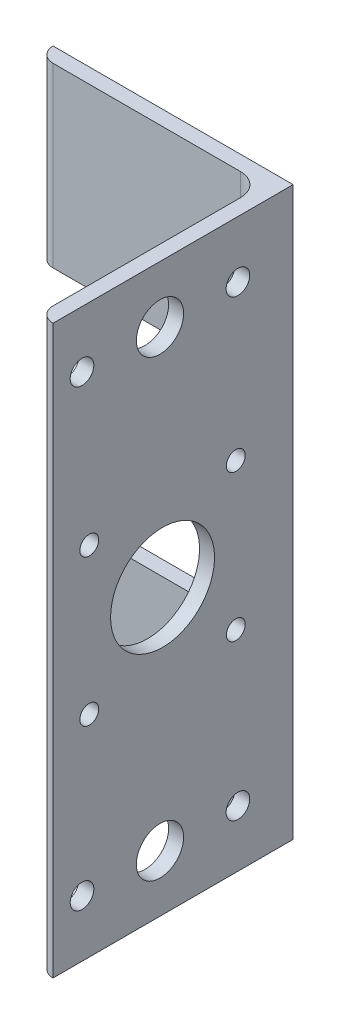
SolidWorks part; units mm, degrees
ref_plane "Alzado" through (0, 0, 0) normal (0, 0, 1) x (1, 0, 0)
ref_plane "Planta" through (0, 0, 0) normal (0, 1, 0) x (1, 0, 0)
ref_plane "Vista lateral" through (0, 0, 0) normal (1, 0, 0) x (0, 0, -1)
sketch "Croquis1" plane through (0, 0, 0) normal (0, 0, 1) x (1, 0, 0)
  line L0 (0, 0) -> (0, 120)
  dimension "D1" = 120
other "Hierro angular 2 X 2 X 0.125(1)"
ref_plane "Plano1" through (0, 0, 0) normal (0, 1, 0) x (-1, 0, 0)
sketch "Sketch1" plane through (0, 0, 0) normal (0, 1, 0) x (-1, 0, 0)
  line L0 (0, 0) -> (0, 50.8)
  line L1 (0, 50.8) -> (0.0051, 50.8)
  line L2 (3.175, 47.6301) -> (3.175, 7.9375)
  line L3 (7.9375, 3.175) -> (47.6301, 3.175)
  line L4 (50.8, 0.0051) -> (50.8, 0)
  line L5 (50.8, 0) -> (0, 0)
  arc A0 (50.8, 0.0051) -> (47.6301, 3.175) centre (47.6301, 0.0051) ccw
  arc A1 (0.0051, 50.8) -> (3.175, 47.6301) centre (0.0051, 47.6301) cw
  arc A2 (7.9375, 3.175) -> (3.175, 7.9375) centre (7.9375, 7.9375) cw
  point P10 (25.4, 0)
  point P14 (0, 25.4)
  point P15 (3.175, 25.4)
  point P16 (25.4, 3.175)
  point P17 (3.175, 50.8)
  point P18 (50.8, 3.175)
  point P19 (0, 0)
  dimension "D2" = 0.0051
  dimension "Radius_1" = 4.7625
  dimension "D1" = 3.175
  dimension "H_leg" = 50.8
sketch "Croquis3" plane through (0, 0, 0) normal (0, 0, -1) x (-1, 0, 0)
  line L0 (3.175, 120) -> (3.175, 0) construction
  line L1 (3.175, 120) -> (3.175, 0) construction
  line L2 (50.8, 60) -> (3.175, 60) construction
  line L3 (50.8, 120) -> (50.8, 0) construction
  line L5 (3.175, 82.5) -> (50.8, 82.5)
  line L6 (3.175, 82.5) -> (3.175, 37.5)
  line L7 (3.175, 37.5) -> (50.8, 37.5)
  line L8 (50.8, 82.5) -> (50.8, 37.5)
  line L9 (3.175, 82.5) -> (50.8, 37.5) construction
  line L10 (3.175, 37.5) -> (50.8, 82.5) construction
  point P6 (26.9875, 60)
  dimension "D1" = 45
extrude "Cortar-Extruir1" cut sketch "Croquis3" against normal blind 10
sketch "Croquis4" plane through (-3.175, 0, 0) normal (-1, 0, 0) x (0, 0, 1)
  line L0 (47.6301, 60) -> (0, 60) construction
  line L1 (47.6301, 120) -> (47.6301, 0) construction
  line L2 (0, 82.5) -> (0, 37.5) construction
  line L3 (3.175, 37.5) -> (3.175, 0) construction
  line L4 (3.175, 37.5) -> (3.175, 0)
  line L5 (3.175, 12) -> (66.2986, 12) construction
  line L6 (28.175, 0) -> (28.175, 21.3337) construction
  line L7 (7.9375, 0) -> (47.6301, 0) construction
  line L8 (44.675, 12) -> (11.675, 12) construction
  circle A0 centre (28.175, 12) radius 5
  circle A1 centre (11.675, 12) radius 2.5
  circle A2 centre (44.675, 12) radius 2.5
  circle A3 centre (44.675, 108) radius 2.5
  circle A4 centre (28.175, 108) radius 5
  circle A5 centre (11.675, 108) radius 2.5
  point P19 (28.175, 12)
  dimension "D3" = 5
  dimension "D4" = 10
  dimension "D1" = 12
  dimension "D2" = 25
  dimension "D5" = 33
extrude "Cortar-Extruir2" cut sketch "Croquis4" against normal blind 10 contours A0 | A1 | A2 | A3 | A4 | A5
sketch "Croquis5" plane through (-3.175, 0, 0) normal (-1, 0, 0) x (0, 0, 1)
  line L0 (0, 60) -> (47.6301, 60) construction
  line L1 (0, 82.5) -> (0, 37.5) construction
  line L2 (47.6301, 120) -> (47.6301, 0) construction
  line L4 (12.1301, 75.5) -> (43.1301, 75.5) construction
  line L5 (12.1301, 75.5) -> (12.1301, 44.5) construction
  line L6 (12.1301, 44.5) -> (43.1301, 44.5) construction
  line L7 (43.1301, 75.5) -> (43.1301, 44.5) construction
  line L8 (12.1301, 75.5) -> (43.1301, 44.5) construction
  line L9 (12.1301, 44.5) -> (43.1301, 75.5) construction
  circle A0 centre (43.1301, 75.5) radius 2
  circle A1 centre (43.1301, 44.5) radius 2
  circle A2 centre (12.1301, 44.5) radius 2
  circle A3 centre (12.1301, 75.5) radius 2
  circle A4 centre (27.6301, 60) radius 11
  point P6 (27.6301, 60)
  dimension "D3" = 4
  dimension "D4" = 22
  dimension "D1" = 31
  dimension "D2" = 31
  dimension "D5" = 20
extrude "Cortar-Extruir3" cut sketch "Croquis5" against normal up to surface (3.175 mm away) up to face at (0, 12, 14.175)
ref_plane "Plano2" through (0, 60, 0) normal (0, -1, 0) x (-1, 0, 0)
